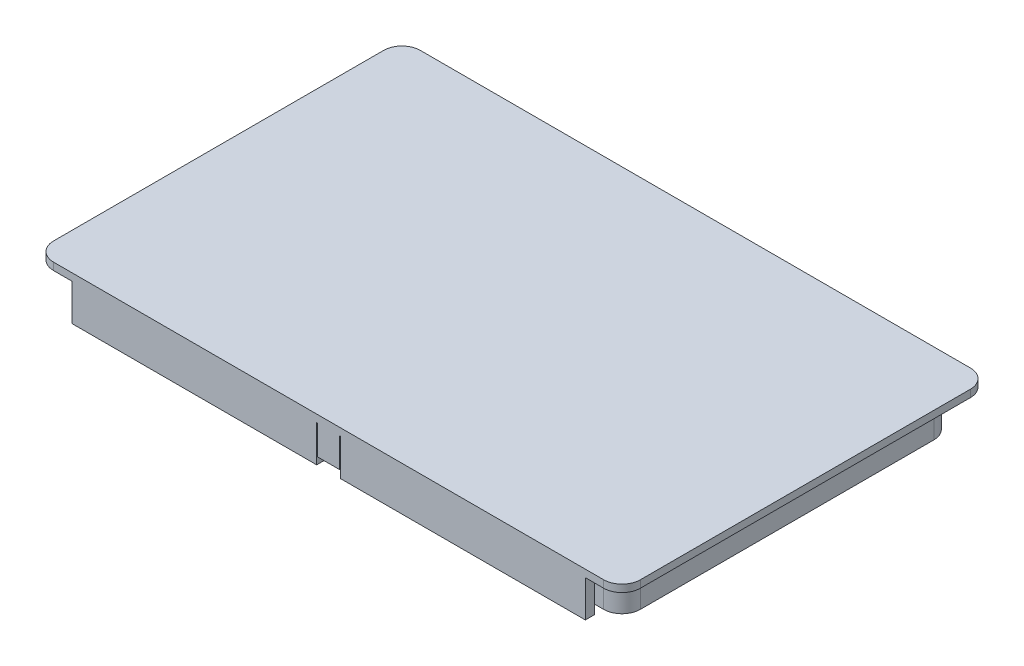
SolidWorks part; units mm, degrees
ref_plane "Front Plane" through (0, 0, 0) normal (0, 0, 1) x (1, 0, 0)
ref_plane "Top Plane" through (0, 0, 0) normal (0, 1, 0) x (1, 0, 0)
ref_plane "Right Plane" through (0, 0, 0) normal (1, 0, 0) x (0, 0, -1)
sketch "Sketch3" plane through (0, 0, 0) normal (0, 1, 0) x (1, 0, 0)
  line L1 (75, -50) -> (-75, -50)
  line L2 (80, -45) -> (80, 45)
  line L3 (75, 50) -> (-75, 50)
  line L4 (-80, -45) -> (-80, 45)
  line L5 (80, -50) -> (-80, 50) construction
  line L6 (80, 50) -> (-80, -50) construction
  arc A0 (75, -50) -> (80, -45) centre (75, -45) ccw
  arc A1 (-75, -50) -> (-80, -45) centre (-75, -45) cw
  arc A2 (80, 45) -> (75, 50) centre (75, 45) ccw
  arc A3 (-75, 50) -> (-80, 45) centre (-75, 45) ccw
  point P0 (0, 0)
  point P18 (0, 0)
  dimension "D3" = 5
  dimension "D1" = 160
  dimension "D2" = 100
extrude "Boss-Extrude1" add sketch "Sketch3" against normal blind 12 contours L4 A3 L3 A2 L2 A0 L1 A1
sketch "Sketch6" plane through (0, -12, 0) normal (0, -1, 0) x (1, 0, 0)
  line L0 (75, 50) -> (-75, 50) construction
  line L1 (70, -45) -> (-70, -45)
  line L2 (75, -40) -> (75, 40)
  line L3 (70, 45) -> (-70, 45)
  line L4 (-75, -40) -> (-75, 40)
  line L5 (75, -45) -> (-75, 45) construction
  line L6 (75, 45) -> (-75, -45) construction
  line L7 (-70, 50) -> (70, 50)
  line L8 (-70, 50) -> (-70, 47.5)
  line L9 (-70, 47.5) -> (70, 47.5)
  line L10 (70, 50) -> (70, 47.5)
  line L11 (-80, 45) -> (-80, -45) construction
  line L12 (80, 45) -> (80, -45) construction
  line L13 (75, -50) -> (-75, -50) construction
  line L14 (-70, -50) -> (70, -50)
  line L15 (-70, -50) -> (-70, -47.5)
  line L16 (-70, -47.5) -> (70, -47.5)
  line L17 (70, -50) -> (70, -47.5)
  arc A0 (-70, -45) -> (-75, -40) centre (-70, -40) cw
  arc A1 (70, -45) -> (75, -40) centre (70, -40) ccw
  arc A2 (75, 40) -> (70, 45) centre (70, 40) ccw
  arc A3 (-70, 45) -> (-75, 40) centre (-70, 40) ccw
  point P0 (0, 0)
  point P26 (70, 48.75)
  dimension "D3" = 5
  dimension "D1" = 150
  dimension "D2" = 90
  dimension "D4" = 2.5
  dimension "D5" = 10
  dimension "D6" = 10
  dimension "D7" = 2.5
  dimension "D8" = 10
  dimension "D9" = 10
extrude "Cut-Extrude1" cut sketch "Sketch6" against normal blind 10 flip side to cut
sketch "Sketch7" plane through (0, -12, 0) normal (0, -1, 0) x (1, 0, 0)
  line L1 (70, -40) -> (-70, -40)
  line L2 (70, -40) -> (70, 40)
  line L3 (70, 40) -> (-70, 40)
  line L4 (-70, -40) -> (-70, 40)
  line L5 (70, -40) -> (-70, 40) construction
  line L6 (70, 40) -> (-70, -40) construction
  point P0 (0, 0)
  dimension "D1" = 140
  dimension "D2" = 80
extrude "Cut-Extrude2" cut sketch "Sketch7" against normal blind 10
sketch "Sketch13" plane through (0, 0, -50) normal (0, 0, -1) x (-1, 0, 0)
  line L0 (-70, -12) -> (70, -12) construction
  line L1 (-3.25, -12) -> (3.25, -12)
  line L2 (-3.25, -12) -> (-3.25, -2)
  line L3 (-3.25, -2) -> (3.25, -2)
  line L4 (3.25, -12) -> (3.25, -2)
  line L5 (0, 6.6) -> (0, -6.6) construction
  dimension "D1" = 6.5
  dimension "D2" = 10
  dimension "D3" = 3.25
extrude "Cut-Extrude3" cut sketch "Sketch13" against normal blind 5
sketch "Sketch14" plane through (0, 0, 0) normal (1, 0, 0) x (0, 0, -1)
  line L0 (50, -2) -> (50, -5.8)
  line L1 (50, -2) -> (50, -12) construction
  line L3 (49.25, -5.85) -> (48.5, -5.1)
  line L4 (48.5, -5.1) -> (48.5, -4.6)
  line L5 (48.5, -4.6) -> (49, -4.6)
  line L6 (49, -4.6) -> (49, -2)
  line L7 (45, -2) -> (50, -2) construction
  line L8 (49, -2) -> (50, -2)
  line L9 (49.25, -5.85) -> (49.25, -10)
  line L10 (49.25, -10) -> (50, -10)
  line L11 (50, -10) -> (50, -5.8)
  dimension "D1" = 3.8
  dimension "D2" = 1.5
  dimension "D3" = 4.2
  dimension "D4" = 1
  dimension "D5" = 135
  dimension "D6" = 0.5
  dimension "D7" = 0.75
extrude "Boss-Extrude2" add sketch "Sketch14" along normal mid plane 6
mirror "Mirror1" about plane through (0, 0, 0) normal (0, 0, 1) of "Boss-Extrude2", "Cut-Extrude3"
